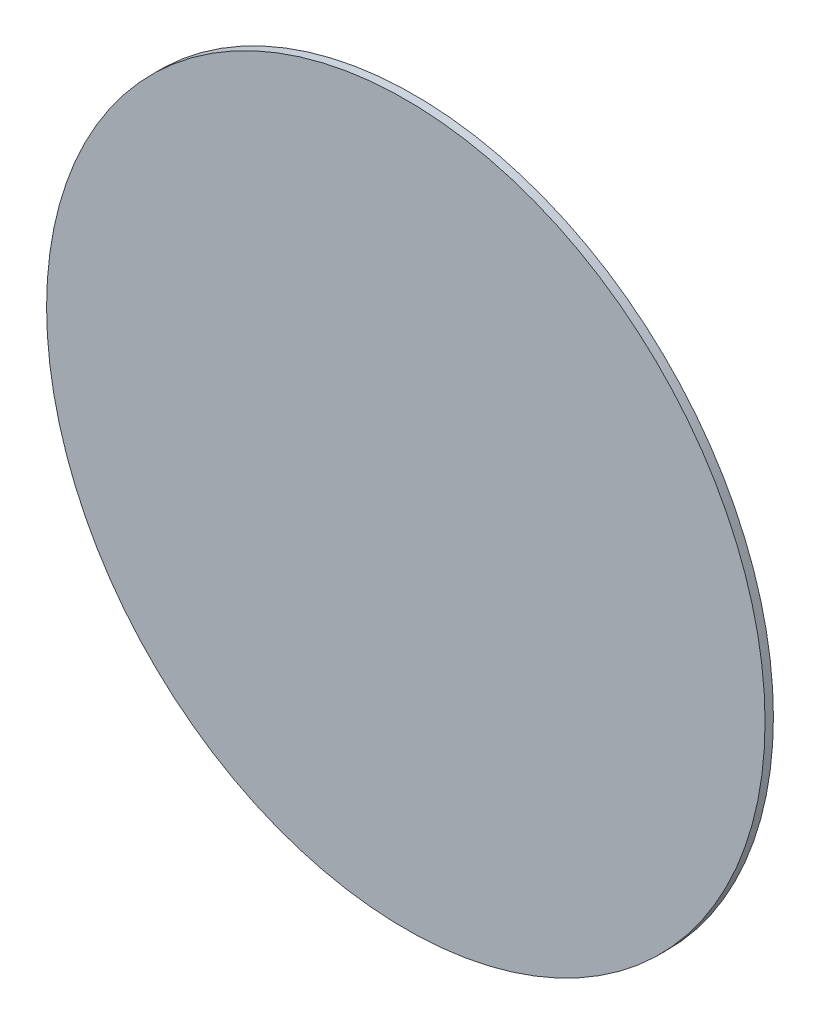
SolidWorks part; units mm, degrees
ref_plane "Front Plane" through (0, 0, 0) normal (0, 0, 1) x (1, 0, 0)
ref_plane "Top Plane" through (0, 0, 0) normal (0, 1, 0) x (1, 0, 0)
ref_plane "Right Plane" through (0, 0, 0) normal (1, 0, 0) x (0, 0, -1)
sketch "Sketch2" plane through (0, 0, 0) normal (0, 0, 1) x (1, 0, 0)
  circle A0 centre (0, 0) radius 107.5
  dimension "D1" = 215
extrude "Boss-Extrude1" add sketch "Sketch2" along normal blind 2.5
